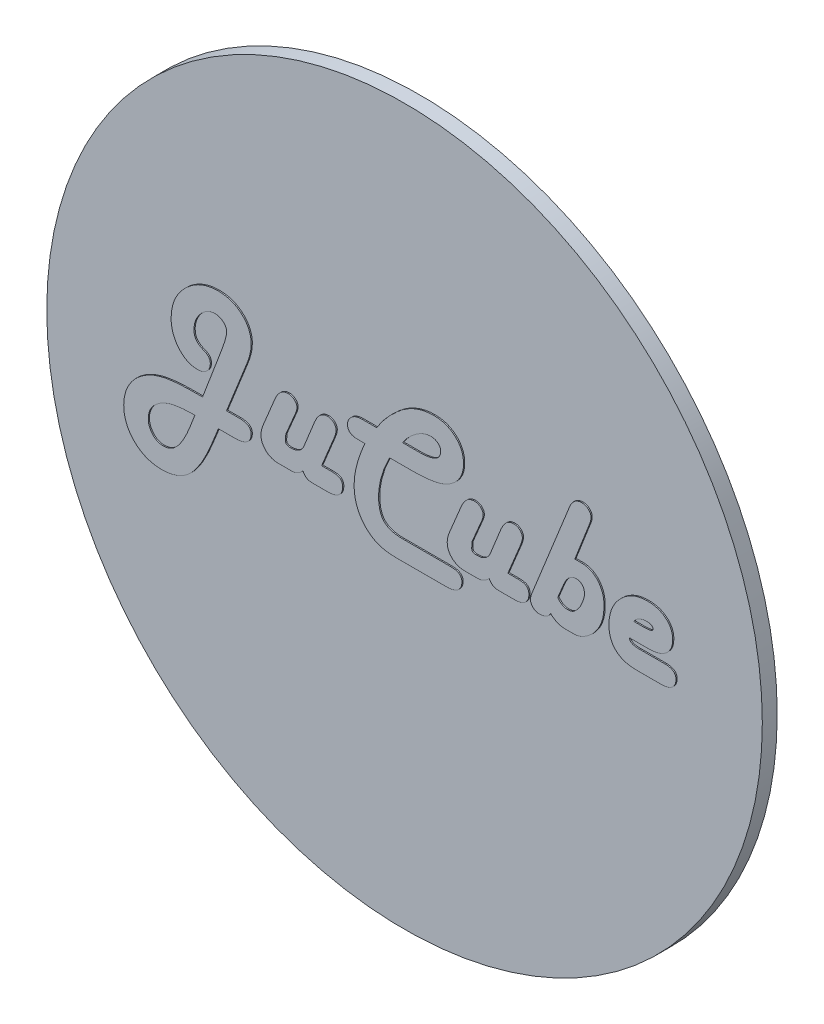
SolidWorks part; units mm, degrees
ref_plane "Front Plane" through (0, 0, 0) normal (0, 0, 1) x (1, 0, 0)
ref_plane "Top Plane" through (0, 0, 0) normal (0, 1, 0) x (1, 0, 0)
ref_plane "Right Plane" through (0, 0, 0) normal (1, 0, 0) x (0, 0, -1)
sketch "Sketch2" plane through (0, 0, 0) normal (0, 0, 1) x (1, 0, 0)
  circle A0 centre (0, 0) radius 76.2
  dimension "D1" = 152.4
extrude "Boss-Extrude1" add sketch "Sketch2" along normal blind 3.175
sketch "Sketch3" plane through (0, 0, 3.175) normal (0, 0, 1) x (1, 0, 0)
  text T0 "JuCube" font "Harlow Solid Italic" height 25.4
extrude "Boss-Extrude2" add sketch "Sketch3" along normal blind 0.254
